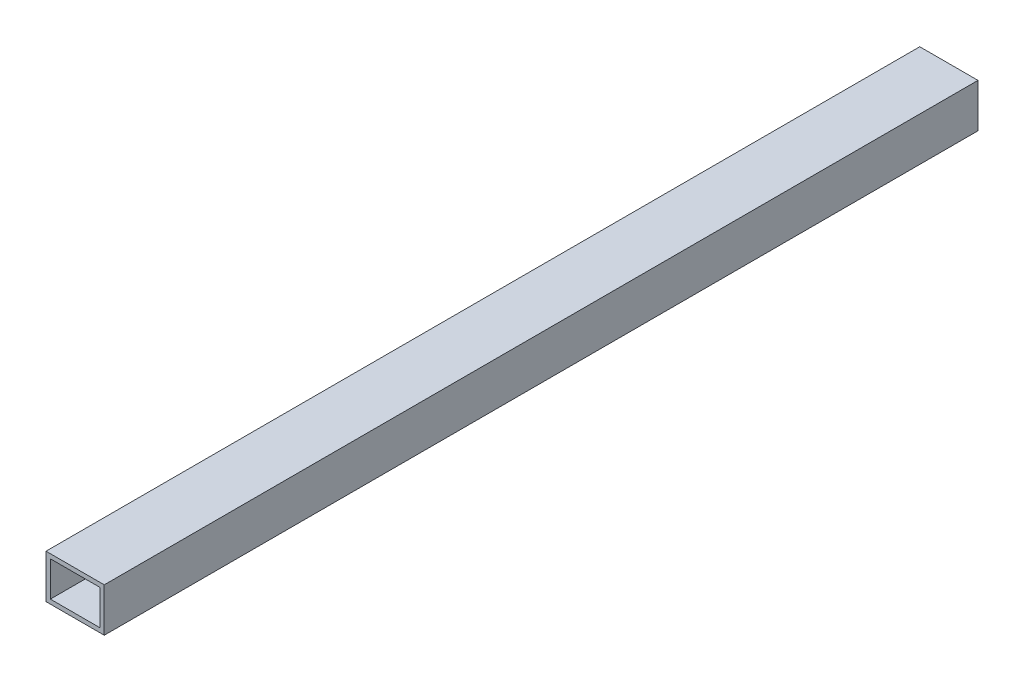
SolidWorks part; units mm, degrees
ref_plane "Front Plane" through (0, 0, 0) normal (0, 0, 1) x (1, 0, 0)
ref_plane "Top Plane" through (0, 0, 0) normal (0, 1, 0) x (1, 0, 0)
ref_plane "Right Plane" through (0, 0, 0) normal (1, 0, 0) x (0, 0, -1)
sketch "Croquis1" plane through (0, 0, 0) normal (1, 0, 0) x (0, 0, -1)
  line L0 (-300, -15) -> (-300, 15)
  line L1 (-300, -15) -> (300, -15)
  line L2 (-300, 15) -> (300, 15)
  line L3 (300, -15) -> (300, 15)
  line L4 (-300, -15) -> (300, 15) construction
  line L5 (-300, 15) -> (300, -15) construction
  point P1 (0, 0)
  dimension "D1" = 600
  dimension "D2" = 30
extrude "Saliente-Extruir1" add sketch "Croquis1" along normal blind 40
sketch "Croquis2" plane through (0, 0, 300) normal (0, 0, 1) x (1, 0, 0)
  line L0 (3, -12) -> (37, -12)
  line L1 (3, -12) -> (3, 12)
  line L2 (37, -12) -> (37, 12)
  line L3 (3, 12) -> (37, 12)
  line L4 (3, -12) -> (37, 12) construction
  line L5 (37, -12) -> (3, 12) construction
  line L6 (40, 15) -> (40, -15) construction
  line L7 (40, 15) -> (0, 15) construction
  line L8 (0, 15) -> (0, -15) construction
  line L9 (40, -15) -> (0, -15) construction
  point P1 (20, 0)
  dimension "D1" = 3
  dimension "D2" = 3
  dimension "D3" = 3
  dimension "D4" = 3
extrude "Cortar-Extruir1" cut sketch "Croquis2" against normal blind 890
